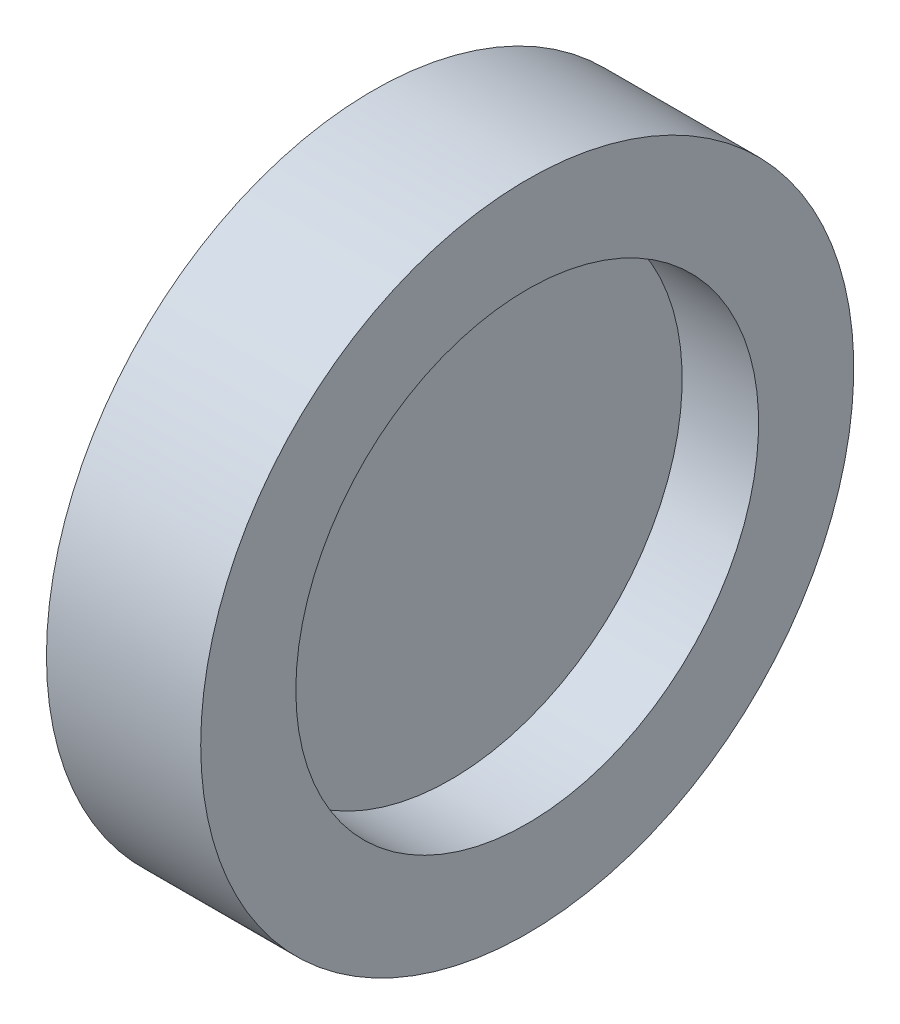
SolidWorks part; units mm, degrees
ref_plane "前视基准面" through (0, 0, 0) normal (0, 0, 1) x (1, 0, 0)
ref_plane "上视基准面" through (0, 0, 0) normal (0, 1, 0) x (1, 0, 0)
ref_plane "右视基准面" through (0, 0, 0) normal (1, 0, 0) x (0, 0, -1)
sketch "草图1" plane through (0, 0, 0) normal (0, 0, 1) x (1, 0, 0)
  line L0 (-0.027, 9) -> (-0.027, 0)
  line L2 (-0.027, 9) -> (0.027, 9)
  line L3 (-0.027, 0) -> (0.027, 0)
  line L4 (0.027, 9) -> (0.027, 0)
revolve "旋转2" add sketch "草图1" angle 360 about L3
sketch "草图4" plane through (0, 0, 0) normal (0, 0, 1) x (1, 0, 0)
  line L0 (-3, 12.7) -> (3, 12.7)
  line L1 (3, 12.7) -> (3, 9)
  line L2 (3, 9) -> (-3, 9)
  line L3 (0.027, 9) -> (-0.027, 9) construction
  line L4 (-3, 9) -> (-3, 12.7)
  line L5 (0, 9) -> (0, 12.7) construction
  line L6 (-1.6142, 0) -> (1.5903, 0) construction
revolve "旋转3" add sketch "草图4" angle 360 about L6
equation "\"D1@草图4\"=\"D1@草图1\""
